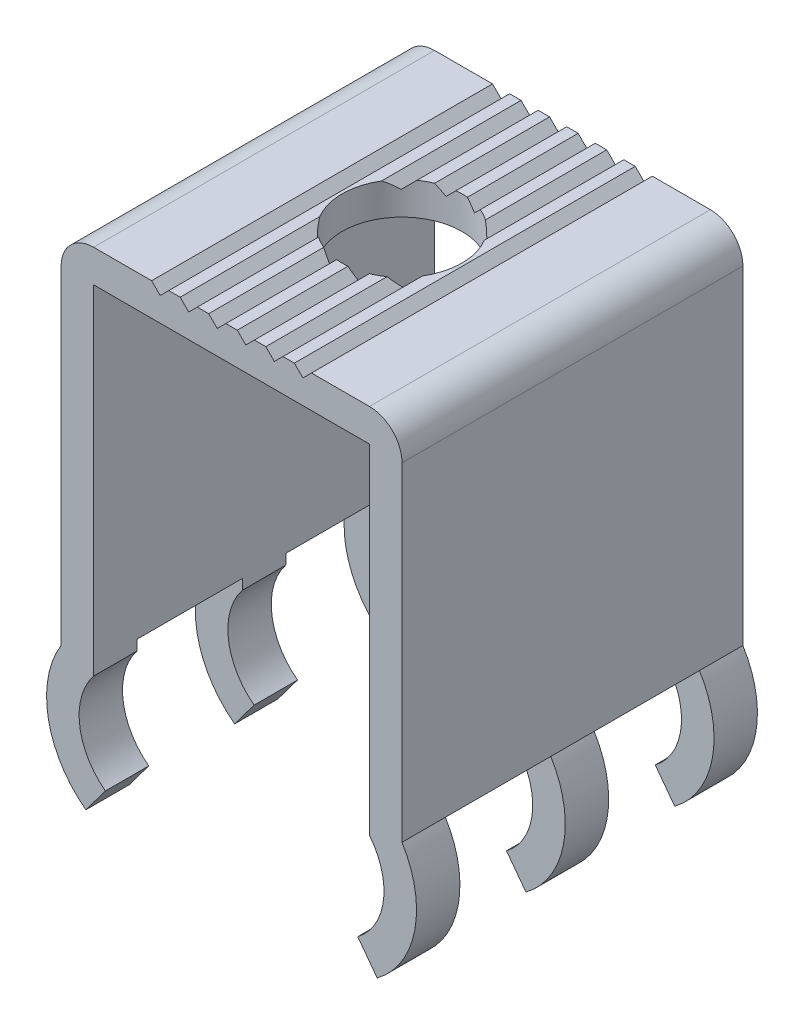
SolidWorks part; units mm, degrees
ref_plane "Front Plane" through (0, 0, 0) normal (0, 0, 1) x (1, 0, 0)
ref_plane "Top Plane" through (0, 0, 0) normal (0, 1, 0) x (1, 0, 0)
ref_plane "Right Plane" through (0, 0, 0) normal (1, 0, 0) x (0, 0, -1)
sketch "Sketch1" plane through (0, 0, 0) normal (0, 1, 0) x (1, 0, 0)
  line L1 (-5.97, 5.97) -> (5.97, 5.97)
  line L2 (-5.97, 5.97) -> (-5.97, -5.97)
  line L3 (-5.97, -5.97) -> (5.97, -5.97)
  line L4 (5.97, 5.97) -> (5.97, -5.97)
  point P5 (5.97, 0)
  point P7 (0, 5.97)
  dimension "D1" = 11.94
extrude "Boss-Extrude1" add sketch "Sketch1" along normal blind 1.14
sketch "Sketch4" plane through (0, 0, 5.97) normal (0, 0, 1) x (1, 0, 0)
  line L0 (0, 0) -> (0, 1.14) construction
  line L1 (0.2, 1.14) -> (0.5, 0.84)
  line L2 (-5.97, 1.14) -> (5.97, 1.14) construction
  line L3 (0.5, 0.84) -> (0.8, 1.14)
  line L4 (-5.97, 0) -> (5.97, 0) construction
  line L5 (-0.5, 0.84) -> (-0.2, 1.14)
  line L6 (-0.8, 1.14) -> (-0.5, 0.84)
  line L7 (-0.8, 1.14) -> (-0.2, 1.14)
  line L8 (0.2, 1.14) -> (0.8, 1.14)
  dimension "D1" = 0.3
  dimension "D3" = 1
  dimension "D4" = 0.5
  dimension "D2" = 2
extrude "Cut-Extrude2" cut sketch "Sketch4" against normal through all
pattern_linear "LPattern1" count 2 spacing 2 along (1, 0, 0) count 2 spacing 2 along (-1, 0, 0) of "Cut-Extrude2"
sketch "Sketch7" plane through (0, 0, 0) normal (0, -1, 0) x (1, 0, 0)
  line L0 (5.97, -5.97) -> (-5.97, -5.97) construction
  line L1 (-5.97, 5.97) -> (-4.83, 5.97)
  line L2 (-5.97, 5.97) -> (-5.97, -5.97)
  line L3 (-5.97, -5.97) -> (-4.83, -5.97)
  line L4 (-4.83, 5.97) -> (-4.83, -5.97)
  line L6 (5.97, 5.97) -> (4.83, 5.97)
  line L7 (5.97, 5.97) -> (5.97, -5.97)
  line L8 (5.97, -5.97) -> (4.83, -5.97)
  line L9 (4.83, 5.97) -> (4.83, -5.97)
  dimension "D1" = 1.14
  dimension "D2" = 1.14
extrude "Boss-Extrude2" add sketch "Sketch7" along normal blind 11.51
sketch "Sketch6" plane through (0, 0, 5.97) normal (0, 0, 1) x (1, 0, 0)
  line L0 (-4.83, -11.51) -> (-4.83, -11.8681)
  line L1 (-4.83, -11.51) -> (-5.97, -11.51)
  line L3 (-4.83, -11.8681) -> (-5.97, -11.51) construction
  line L4 (-4.4189, -15.1473) -> (-5.1019, -16.06)
  arc A0 (-4.83, -11.8681) -> (-4.4189, -15.1473) centre (-3.0434, -13.3095) ccw
  arc A1 (-5.97, -11.51) -> (-5.1019, -16.06) centre (-3.0434, -13.3095) ccw
  dimension "D4" = 1.14
  dimension "D1" = 17.2
  dimension "D3" = 1.14
extrude "Boss-Extrude3" add sketch "Sketch6" against normal blind 1.52
pattern_linear "LPattern3" count 3 spacing 5.21 along (0, 0, -1) of "Boss-Extrude3"
mirror "Mirror1" about plane through (0, 0, 0) normal (1, 0, 0) of "LPattern3", "Boss-Extrude3"
fillet "Fillet2" radius 1.14 2 edges at (5.97, 1.14, 0) (-5.97, 1.14, 0)
hole_wizard "M5x0.8 Tapped Hole2" positions "Sketch10" profile "Sketch9" tap size "M5x0.8" standard "ANSI Metric" end condition through all
sketch "Sketch10" plane through (0, 0, 0) normal (0, 1, 0) x (1, 0, 0)
  point P0 (0, 0)
sketch "Sketch9" plane through (0, 0, 0) normal (1, 0, 0) x (0, 0, -1)
  line L0 (0, 0) -> (0, 1.14)
  line L1 (0, 1.14) -> (2.1, 1.14)
  line L2 (2.1, 1.14) -> (2.1, 0)
  line L5 (2.1, 0) -> (0, 0)
  line L11 (0, -6.35) -> (0, 107.95) construction
  dimension "Thru Tap Drill Dia." = 4.2
  dimension "Thru Tap Drill Depth" = 1.14
cosmetic thread "Hole Thread4" parameters "D2"=5
